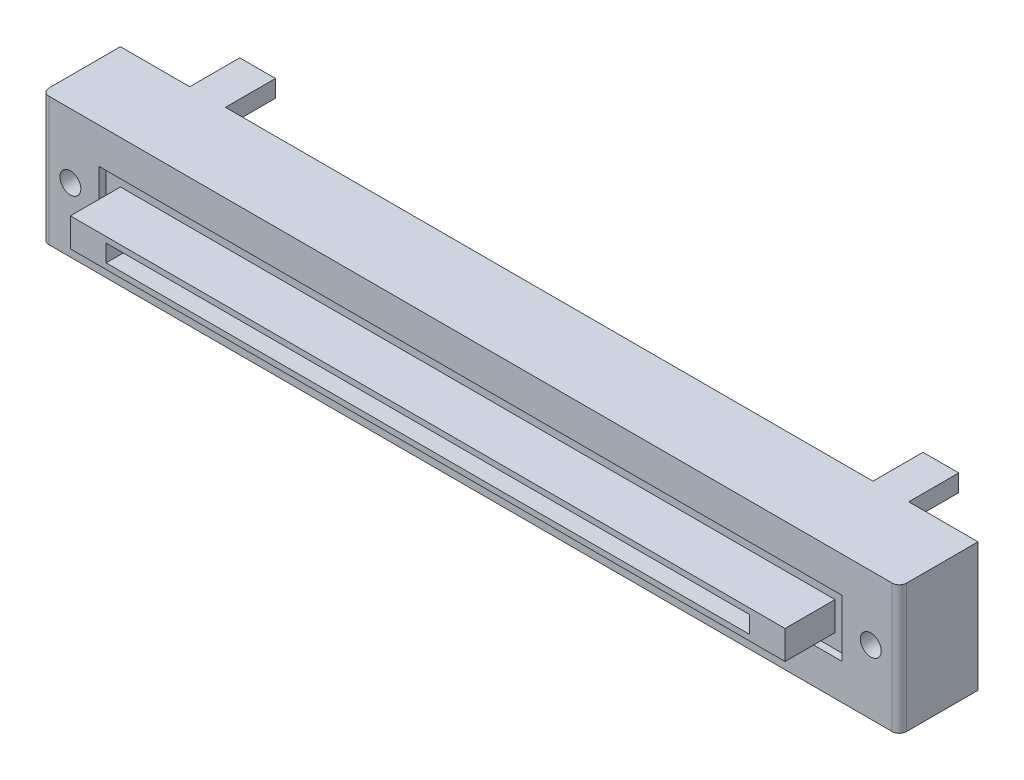
SolidWorks part; units mm, degrees
ref_plane "Ebene vorne" through (0, 0, 0) normal (0, 0, 1) x (1, 0, 0)
ref_plane "Ebene oben" through (0, 0, 0) normal (0, 1, 0) x (1, 0, 0)
ref_plane "Ebene rechts" through (0, 0, 0) normal (1, 0, 0) x (0, 0, -1)
sketch "Skizze1" plane through (0, 0, 0) normal (0, 0, 1) x (1, 0, 0)
  line L1 (-30, 4.5) -> (30, 4.5)
  line L2 (-30, 4.5) -> (-30, -4.5)
  line L3 (-30, -4.5) -> (30, -4.5)
  line L4 (30, 4.5) -> (30, -4.5)
  line L5 (-30, 4.5) -> (30, -4.5) construction
  line L6 (-30, -4.5) -> (30, 4.5) construction
  point P0 (0, 0)
  dimension "D1" = 60
  dimension "D2" = 9
extrude "body" add sketch "Skizze1" against normal blind 5.5
sketch "Skizze4" plane through (0, 0, 0) normal (0, 0, 1) x (1, 0, 0)
  circle A0 centre (-28, 0) radius 0.7307
  circle A1 centre (28, 0) radius 0.7307
  dimension "D1" = 28
  dimension "D2" = 56
extrude "screw holes" cut sketch "Skizze4" against normal blind 3
sketch "Skizze5" plane through (0, 0, 0) normal (0, 0, 1) x (1, 0, 0)
  line L1 (-26, 2) -> (26, 2)
  line L2 (-26, 2) -> (-26, -2)
  line L3 (-26, -2) -> (26, -2)
  line L4 (26, 2) -> (26, -2)
  line L5 (-26, 2) -> (26, -2) construction
  line L6 (-26, -2) -> (26, 2) construction
  point P0 (0, 0)
  dimension "D1" = 52
  dimension "D2" = 4
extrude "Schnitt-Linear austragen3" cut sketch "Skizze5" against normal blind 0.5
fillet "Verrundung1" radius 0.5 2 edges at (30, 0, 0) (-30, 0, 0)
sketch "pathway of glider" plane through (0, 0, 0) normal (0, 0, 1) x (1, 0, 0)
  line L1 (-25, 1) -> (25, 1)
  line L2 (-25, 1) -> (-25, -1)
  line L3 (-25, -1) -> (25, -1)
  line L4 (25, 1) -> (25, -1)
  line L5 (-25, 1) -> (25, -1) construction
  line L6 (-25, -1) -> (25, 1) construction
  point P0 (0, 0)
  dimension "D1" = 50
  dimension "D2" = 2
extrude "pathway" add sketch "pathway of glider" along normal mid plane 6 separate body
sketch "Skizze7" plane through (0, 0, 3) normal (0, 0, 1) x (1, 0, 0)
  line L1 (-22.5, 0.6) -> (22.5, 0.6)
  line L2 (-22.5, 0.6) -> (-22.5, -0.6)
  line L3 (-22.5, -0.6) -> (22.5, -0.6)
  line L4 (22.5, 0.6) -> (22.5, -0.6)
  line L5 (-22.5, 0.6) -> (22.5, -0.6) construction
  line L6 (-22.5, -0.6) -> (22.5, 0.6) construction
  point P0 (0, 0)
  dimension "D1" = 1.2
  dimension "D2" = 45
extrude "45mm" cut sketch "Skizze7" against normal blind 3
sketch "flap" plane through (0, 0, -5.5) normal (0, 0, -1) x (-1, 0, 0)
  line L0 (30, -3.9) -> (-30, -3.9) construction
  line L1 (30, 4.5) -> (30, -4.5) construction
  line L2 (-30, -4.5) -> (-30, 4.5) construction
  line L3 (30, 3.9) -> (-30, 3.9) construction
  line L4 (30, -4.5) -> (-30, -4.5) construction
  line L5 (-30, 4.5) -> (30, 4.5) construction
  line L7 (-26.35, -3.3) -> (-23.85, -3.3)
  line L8 (-26.35, -3.3) -> (-26.35, -4.5)
  line L9 (-26.35, -4.5) -> (-23.85, -4.5)
  line L10 (-23.85, -3.3) -> (-23.85, -4.5)
  line L11 (-26.35, -3.3) -> (-23.85, -4.5) construction
  line L12 (-26.35, -4.5) -> (-23.85, -3.3) construction
  line L13 (23.85, -3.3) -> (26.35, -3.3)
  line L14 (23.85, -3.3) -> (23.85, -4.5)
  line L15 (23.85, -4.5) -> (26.35, -4.5)
  line L16 (26.35, -3.3) -> (26.35, -4.5)
  line L17 (23.85, -3.3) -> (26.35, -4.5) construction
  line L18 (23.85, -4.5) -> (26.35, -3.3) construction
  line L19 (25.15, 3.3) -> (22.65, 3.3)
  line L20 (25.15, 3.3) -> (25.15, 4.5)
  line L21 (25.15, 4.5) -> (22.65, 4.5)
  line L22 (22.65, 3.3) -> (22.65, 4.5)
  line L23 (25.15, 3.3) -> (22.65, 4.5) construction
  line L24 (25.15, 4.5) -> (22.65, 3.3) construction
  line L25 (-22.65, 3.3) -> (-25.15, 3.3)
  line L26 (-22.65, 3.3) -> (-22.65, 4.5)
  line L27 (-22.65, 4.5) -> (-25.15, 4.5)
  line L28 (-25.15, 3.3) -> (-25.15, 4.5)
  line L29 (-22.65, 3.3) -> (-25.15, 4.5) construction
  line L30 (-22.65, 4.5) -> (-25.15, 3.3) construction
  point P12 (25.1, -3.9)
  point P13 (-25.1, -3.9)
  point P14 (25.1, -3.9)
  point P15 (-25.1, -3.9)
  point P19 (-25.1, -3.9)
  point P21 (25.1, -3.9)
  point P24 (23.9, 3.9)
  point P25 (-23.9, 3.9)
  point P26 (23.9, 3.9)
  point P31 (-23.9, 3.9)
  dimension "D1" = 0.6
  dimension "D2" = 0.6
  dimension "D3" = 50.2
  dimension "D4" = 4.9
  dimension "D5" = 2.5
  dimension "D6" = 2.5
  dimension "D7" = 47.8
  dimension "D8" = 6.1
  dimension "D9" = 2.5
  dimension "D10" = 2.5
extrude "flaps" add sketch "flap" along normal blind 3.5
